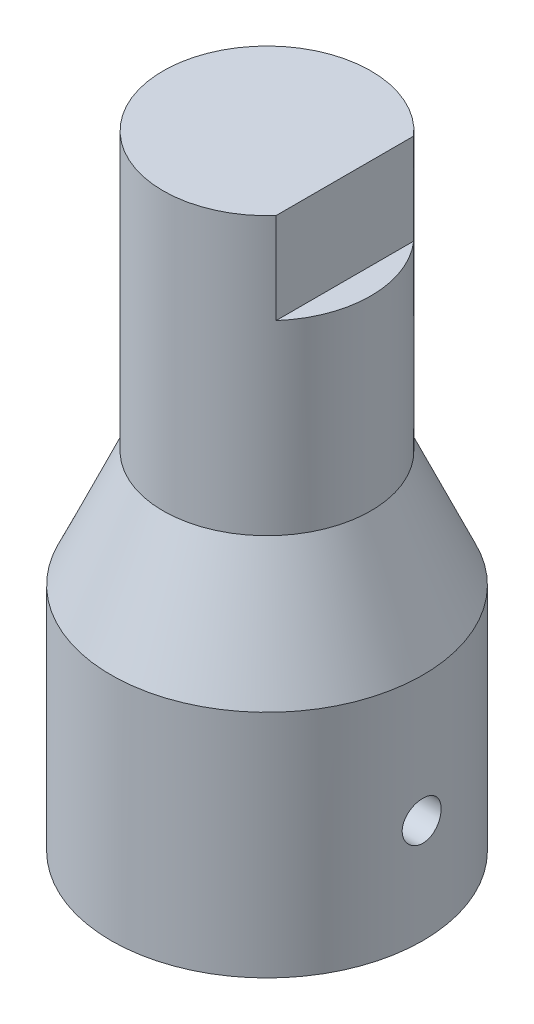
SolidWorks part; units mm, degrees
ref_plane "Front Plane" through (0, 0, 0) normal (0, 0, 1) x (1, 0, 0)
ref_plane "Top Plane" through (0, 0, 0) normal (0, 1, 0) x (1, 0, 0)
ref_plane "Right Plane" through (0, 0, 0) normal (1, 0, 0) x (0, 0, -1)
sketch "Sketch1" plane through (0, 0, 0) normal (0, 1, 0) x (1, 0, 0)
  circle A0 centre (0, 0) radius 9.525
  dimension "D1" = 19.05
extrude "Boss-Extrude1" add sketch "Sketch1" along normal blind 14.06
ref_plane "Plane1" through (0, 14.06, 0) normal (0, 1, 0) x (1, 0, 0)
ref_plane "Plane2" through (0, 38.1, 0) normal (0, 1, 0) x (1, 0, 0)
sketch "Sketch2" plane through (0, 38.1, 0) normal (0, 1, 0) x (1, 0, 0)
  circle A0 centre (0, 0) radius 6.35
  dimension "D1" = 12.7
extrude "Boss-Extrude2" add sketch "Sketch2" against normal blind 16.94 separate body contours A0
loft "Loft1" add section edge at (0, 14.06, 9.525) section edge at (0, 21.16, 6.35)
sketch "Sketch3" plane through (0, 0, 0) normal (0, 0, 1) x (1, 0, 0)
  line L0 (10.4775, 38.1) -> (-10.4775, 38.1) construction
  line L1 (6.35, 21.16) -> (6.35, 38.1) construction
  line L2 (6.35, 38.1) -> (4.76, 38.1)
  line L3 (6.35, 38.1) -> (6.35, 32.54)
  line L4 (6.35, 32.54) -> (4.76, 32.54)
  line L5 (4.76, 38.1) -> (4.76, 32.54)
  line L6 (-6.35, 38.1) -> (-6.35, 21.16) construction
  dimension "D1" = 11.11
  dimension "D2" = 5.56
extrude "Cut-Extrude1" cut sketch "Sketch3" against normal mid plane 16.94
sketch "Sketch4" plane through (0, 0, 0) normal (0, -1, 0) x (1, 0, 0)
  circle A1 centre (0, 0) radius 9.525 construction
  circle A2 centre (-0.795, -0.79) radius 5.555
  point P4 (9.525, 0)
  dimension "D3" = 11.11
  dimension "D1" = 10.32
  dimension "D2" = 0.79
sketch "Sketch5" plane through (0, 0, 0) normal (1, 0, 0) x (0, 0, -1)
  line L0 (-9.525, 0) -> (9.525, 0) construction
  line L1 (0, 0) -> (0, 35.4004) construction
  circle A0 centre (0, 6.35) radius 1.19
  dimension "D1" = 2.38
  dimension "D2" = 6.35
extrude "Cut-Extrude3" cut sketch "Sketch5" along normal blind 14.06
extrude "Cut-Extrude4" cut sketch "Sketch4" against normal blind 14.06 contours A2
